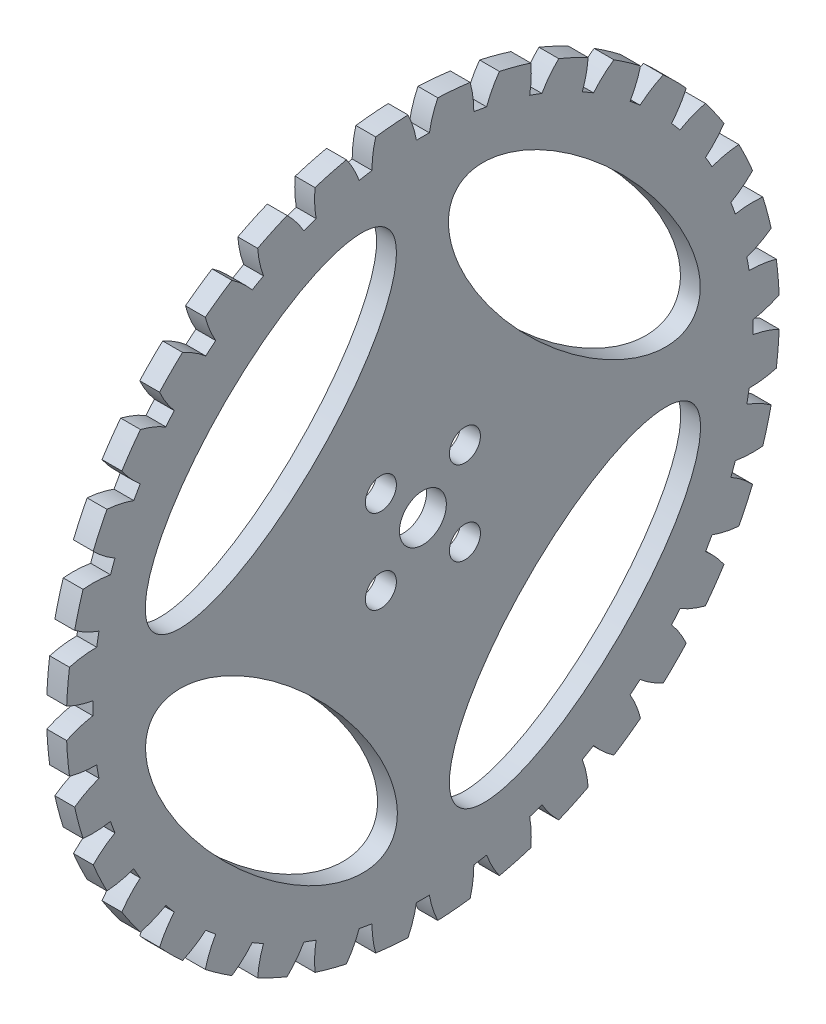
SolidWorks part; units mm, degrees
material "Acrylic (Medium-high impact)"
ref_plane "Ebene vorne" through (0, 0, 0) normal (0, 0, 1) x (1, 0, 0)
ref_plane "Ebene oben" through (0, 0, 0) normal (0, 1, 0) x (1, 0, 0)
ref_plane "Ebene rechts" through (0, 0, 0) normal (1, 0, 0) x (0, 0, -1)
sketch "Skizze1" plane through (0, 0, 0) normal (0, 0, 1) x (1, 0, 0)
  line L0 (-38.0534, 63.75) -> (-41.0534, 63.75)
  line L2 (-41.0534, 13.3) -> (-38.0534, 13.3)
  line L5 (-41.0534, 13.3) -> (-41.0534, 63.75)
  line L8 (-17.6629, 9.75) -> (-37.0534, 9.75) construction
  line L12 (-38.0534, 13.3) -> (-38.0534, 63.75)
  line L25 (-41.0534, 28.75) -> (-41.0534, 26.8663) construction
  dimension "D5" = 108
  dimension "D2" = 7.1
  dimension "D6" = 3
revolve "Rotation1" add sketch "Skizze1" angle 360 about L8
hole_wizard "Ø4.7 (4.7) Durchmesser Bohrung1" positions "Skizze3" profile "Skizze4" hole size "Ø4.7" standard "DIN" end condition through all
sketch "Skizze3" plane through (-41.0534, 11.9687, 19.8689) normal (-1, 0, 0) x (0, 0, 1)
  point P0 (-13.505, -8.5827)
  point P3 (-26.2329, -8.5827)
  point P6 (-26.2329, 4.1452)
  point P9 (-13.505, 4.1452)
sketch "Skizze4" plane through (-41.0534, 3.386, 6.364) normal (0, 1, 0) x (0, 0, 1)
  line L0 (0, 0) -> (0, 3)
  line L1 (0, 3) -> (2.35, 3)
  line L2 (2.35, 3) -> (2.35, 0)
  line L5 (2.35, 0) -> (0, 0)
  line L11 (0, -6.35) -> (0, 107.95) construction
  dimension "Bohrerdurchmesser" = 4.7
  dimension "Bohrungstiefe" = 3
sketch "Skizze5" plane through (-38.0534, 0, 0) normal (1, 0, 0) x (0, 0, -1)
  line L0 (-15.9451, 25.6246) -> (-23.0273, 32.6845) construction
  line L1 (6.364, 3.386) -> (-6.2453, 15.9555) construction
  circle A0 centre (0, 9.75) radius 22.5 construction
  ellipse E0 centre (-23.0273, 32.6845) end of major axis (-5.3776, 50.3901) minor radius 10
  dimension "D1" = 45
  dimension "D3" = 50
  dimension "D4" = 20
extrude "Schnitt-Linear austragen1" cut sketch "Skizze5" against normal up to next (3 mm away)
pattern_circular "Kreismuster1" count 4 over 360 of "Schnitt-Linear austragen1"
ref_plane "Plane1" through (-41.0534, 0, 0) normal (-1, 0, 0) x (0, 0, 1)
sketch "Sketch1" plane through (-38.0534, 0, 0) normal (1, 0, 0) x (0, 0, -1)
  line L0 (0, 9.75) -> (0, 63.75) construction
  line L1 (-2.25, 63.7031) -> (2.25, 63.7031) construction
  line L3 (-2.25, 63.7031) -> (2.25, 63.7031) construction
  line L4 (-2.25, 63.7031) -> (-2.25, 64.0548)
  line L5 (-2.25, 64.0548) -> (2.25, 64.0548)
  line L6 (2.25, 63.7031) -> (2.25, 64.0548)
  circle A0 centre (0, 9.75) radius 54 construction
  circle A1 centre (0, 9.75) radius 50 construction
  arc A2 (0.9834, 59.7403) -> (-0.9834, 59.7403) centre (0, 9.75) ccw
  circle A3 centre (0, 9.75) radius 54 construction
  arc A6 (2.25, 63.7031) -> (0.9834, 59.7403) centre (15.7666, 57.1991) ccw
  arc A7 (-0.9834, 59.7403) -> (-2.25, 63.7031) centre (-15.7666, 57.1991) ccw
  dimension "D2" = 50
  dimension "D3" = 100
  dimension "D6" = 15
  dimension "D4" = 0.3517
  dimension "D5" = 4.5
extrude "Cut-Extrude1" cut sketch "Sketch1" against normal through all
pattern_circular "CirPattern1" count 36 over 360 about axis through (0, 9.75, 0) along (1, 0, 0) of "Cut-Extrude1"
